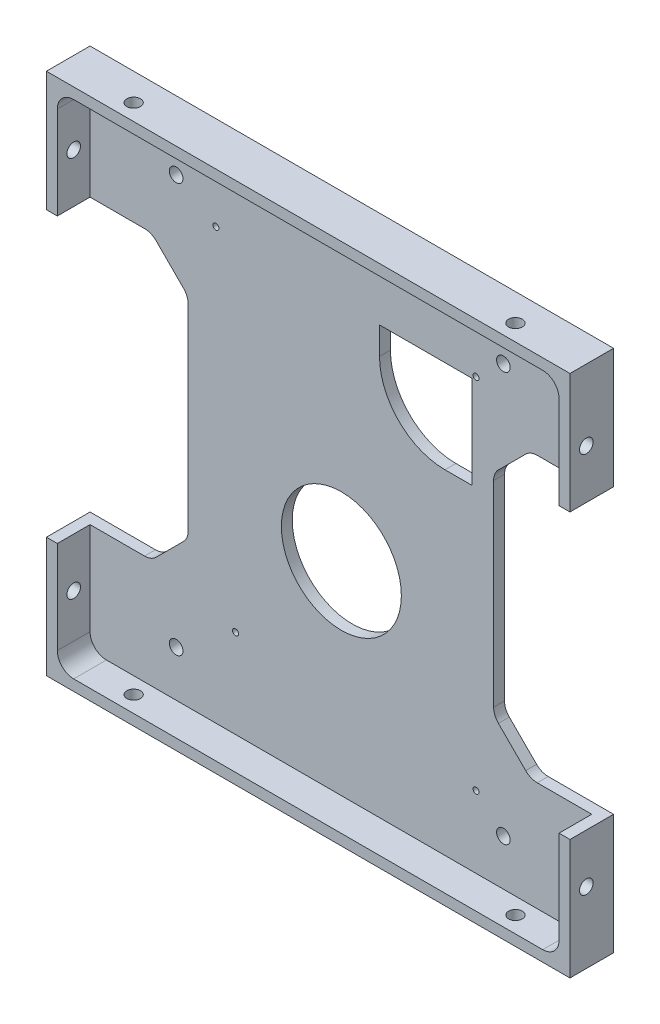
SolidWorks part; units mm, degrees
material "6061-T6 (SS)"
ref_plane "Front" through (0, 0, 0) normal (0, 0, 1) x (1, 0, 0)
ref_plane "Top" through (0, 0, 0) normal (0, 1, 0) x (1, 0, 0)
ref_plane "Right" through (0, 0, 0) normal (1, 0, 0) x (0, 0, -1)
sketch "Sketch1" plane through (0, 0, 0) normal (0, 0, 1) x (1, 0, 0)
  line L1 (-48, -48) -> (48, -48)
  line L2 (-48, -48) -> (-48, 48)
  line L3 (-48, 48) -> (48, 48)
  line L4 (48, -48) -> (48, 48)
  line L5 (-48, -48) -> (48, 48) construction
  line L6 (-48, 48) -> (48, -48) construction
  point P0 (0, 0)
  dimension "D1" = 96
  dimension "D2" = 96
extrude "Boss-Extrude1" add sketch "Sketch1" along normal blind 8
sketch "Sketch2" plane through (0, 0, 8) normal (0, 0, 1) x (1, 0, 0)
  line L1 (46, -46) -> (-46, -46)
  line L2 (46, -46) -> (46, 46)
  line L3 (46, 46) -> (-46, 46)
  line L4 (-46, -46) -> (-46, 46)
  line L5 (46, -46) -> (-46, 46) construction
  line L6 (46, 46) -> (-46, -46) construction
  point P0 (0, 0)
  dimension "D1" = 92
  dimension "D2" = 92
extrude "Component Platform" cut sketch "Sketch2" against normal blind 6
sketch "Sketch3" plane through (0, 0, 2) normal (0, 0, 1) x (1, 0, 0)
  line L1 (-33.8787, -25.1213) -> (-28.8787, -20.1213)
  line L2 (-33.8787, 25.1213) -> (-28.8787, 20.1213)
  line L3 (-28, -18) -> (-28, 18)
  line L4 (-48, -26) -> (-36, -26)
  line L7 (-48, 48) -> (-48, -48) construction
  line L8 (0, -56.7987) -> (0, 73.4321) construction
  line L9 (46, -46) -> (-57.8147, 57.8147) construction
  line L18 (46, 46) -> (-68.5705, -68.5705) construction
  line L23 (-48, 26) -> (-36, 26)
  line L26 (-48, -26) -> (-48, 26)
  line L28 (-48, -48) -> (48, -48) construction
  line L29 (48, -26) -> (48, 26)
  line L30 (48, 26) -> (36, 26)
  line L31 (33.8787, 25.1213) -> (28.8787, 20.1213)
  line L32 (28, -18) -> (28, 18)
  line L33 (33.8787, -25.1213) -> (28.8787, -20.1213)
  line L34 (48, -26) -> (36, -26)
  arc A3 (-28.8787, -20.1213) -> (-28, -18) centre (-31, -18) ccw
  arc A4 (-28.8787, 20.1213) -> (-28, 18) centre (-31, 18) cw
  arc A13 (-33.8787, -25.1213) -> (-36, -26) centre (-36, -23) cw
  arc A15 (-33.8787, 25.1213) -> (-36, 26) centre (-36, 23) ccw
  arc A17 (33.8787, 25.1213) -> (36, 26) centre (36, 23) cw
  arc A18 (28.8787, 20.1213) -> (28, 18) centre (31, 18) ccw
  arc A19 (28.8787, -20.1213) -> (28, -18) centre (31, -18) cw
  arc A20 (33.8787, -25.1213) -> (36, -26) centre (36, -23) ccw
  point P0 (-48, 0)
  point P37 (-48, 0)
  dimension "D2" = 3
  dimension "D3" = 3
  dimension "D4" = 20
  dimension "D6" = 3
  dimension "D7" = 3
  dimension "D8" = 135
  dimension "D5" = 52
  dimension "D9" = 135
  dimension "D10" = 12
  dimension "D11" = 12
  dimension "D12" = 48
extrude "Cable Slots" cut sketch "Sketch3" against normal mid plane 12
ref_plane "Center Y-Plane" through (0, 0, 0) normal (1, 0, 0) x (0, 0, -1)
ref_plane "Center X-Plane" through (0, 0, 0) normal (0, -1, 0) x (-1, 0, 0)
fillet "Inner Corner Fillets" radius 3 4 edges at (46, -46, 5) (-46, -46, 5) (46, 46, 5) (-46, 46, 5)
sketch "Sketch7" plane through (0, 0, 2) normal (0, 0, 1) x (1, 0, 0)
  line L0 (-48, -48) -> (48, -48) construction
  line L4 (48, -48) -> (48, -26) construction
  line L5 (48, 26) -> (48, 48) construction
  line L7 (48, 48) -> (-48, 48) construction
  line L8 (-43, -46) -> (43, -46) construction
  point P1 (-19.32, -29.75)
  point P4 (24.78, -32.85)
  point P5 (24.78, 32.85)
  point P8 (-22.92, 32.85)
  point P12 (24.7, -56.85)
  point P13 (24.7, 48)
  point P14 (-19.4, -48)
  point P15 (48, -32.85)
  point P16 (-48, -32.85)
  point P18 (-19.4, 48)
  point P19 (48, -32.85)
  point P20 (-48, -32.85)
  point P24 (48, 43.7)
  point P25 (-48.7506, 43.7)
  point P27 (48, 32.85)
  point P28 (-23, -48)
  point P29 (-23, 48)
  point P31 (-48.7506, 32.85)
  dimension "D1" = 16.25
  dimension "D2" = 47.7
  dimension "D3" = 15.15
  dimension "D4" = 23.22
  dimension "D5" = 23.22
  dimension "D6" = 44.1
  dimension "D7" = 15.15
  dimension "D8" = 15.15
sketch "Sketch9" plane through (0, 0, 2) normal (0, 0, 1) x (1, 0, 0)
  line L0 (24.08, 32.25) -> (24.08, 15.25)
  line L1 (24.08, 32.25) -> (7.08, 32.25)
  line L3 (24.08, 15.25) -> (19.08, 15.25)
  line L4 (7.08, 27.25) -> (7.08, 32.25)
  line L6 (48, 26) -> (48, 48) construction
  line L8 (48, 48) -> (-48, 48) construction
  arc A0 (7.08, 27.25) -> (19.08, 15.25) centre (19.08, 27.25) ccw
  dimension "D1" = 12
  dimension "D2" = 17
  dimension "D3" = 17
  dimension "D4" = 15.75
  dimension "D5" = 23.92
sketch "Sketch11" plane through (48, 0, 0) normal (1, 0, 0) x (0, 0, -1)
  line L0 (-5, -48) -> (-5, 48) construction
  line L1 (-8, -48) -> (0, -48) construction
  line L2 (-8, 48) -> (0, 48) construction
  line L3 (-8, -48) -> (-8, -26) construction
  dimension "D1" = 3
sketch "Sketch12" plane through (0, 48, 0) normal (0, 1, 0) x (1, 0, 0)
  line L0 (-48, -5) -> (48, -5) construction
  line L1 (-48, -8) -> (-48, 0) construction
  line L2 (48, -8) -> (48, 0) construction
  line L3 (48, -8) -> (-48, -8) construction
  dimension "D1" = 3
hole_wizard "M3x0.5 Tapped Hole1" positions "Sketch13" profile "Sketch14" tap size "M3x0.5" standard "ANSI Metric"
sketch "Sketch13" plane through (48, 0, 0) normal (1, 0, 0) x (0, 0, -1)
  line L0 (-5, -48) -> (-5, 48) construction
  point P0 (-5, -35)
  point P4 (-5, 35)
  dimension "D1" = 70
  dimension "D2" = 35
sketch "Sketch14" plane through (48, -35, 5) normal (0, 1, 0) x (0, 0, -1)
  line L0 (0, 0) -> (0, 10.7511)
  line L1 (0, 10.7511) -> (1.25, 10)
  line L2 (1.25, 10) -> (1.25, 0)
  line L5 (1.25, 0) -> (0, 0)
  line L10 (0, 10.7511) -> (-1.25, 10) construction
  line L11 (0, -6.35) -> (0, 107.95) construction
  dimension "Tap Drill Dia." = 2.5
  dimension "Tap Drill Depth" = 10
  dimension "Drill Angle" = 118
hole_wizard "M3x0.5 Tapped Hole2" positions "Sketch15" profile "Sketch16" tap size "M3x0.5" standard "ANSI Metric"
sketch "Sketch15" plane through (0, 48, 0) normal (0, 1, 0) x (1, 0, 0)
  line L0 (-48, -5) -> (48, -5) construction
  point P0 (35, -5)
  point P4 (-35, -5)
  dimension "D1" = 70
  dimension "D2" = 35
sketch "Sketch16" plane through (35, 48, 5) normal (1, 0, 0) x (0, 0, 1)
  line L0 (0, 0) -> (0, 10.7511)
  line L1 (0, 10.7511) -> (1.25, 10)
  line L2 (1.25, 10) -> (1.25, 0)
  line L5 (1.25, 0) -> (0, 0)
  line L10 (0, 10.7511) -> (-1.25, 10) construction
  line L11 (0, -6.35) -> (0, 107.95) construction
  dimension "Tap Drill Dia." = 2.5
  dimension "Tap Drill Depth" = 10
  dimension "Drill Angle" = 118
mirror "Mirror1" about plane through (0, 0, 0) normal (1, 0, 0) of "M3x0.5 Tapped Hole1"
mirror "Mirror2" about plane through (0, 0, 0) normal (0, -1, 0) of "M3x0.5 Tapped Hole2"
sketch "Sketch22" plane through (0, 0, 2) normal (0, 0, 1) x (1, 0, 0)
  line L0 (-46, -26) -> (-46, -43) construction
  line L1 (-43, -46) -> (43, -46) construction
  line L5 (-46, 43) -> (-46, 26) construction
  line L13 (43, 46) -> (-43, 46) construction
  point P0 (-30.21, -37.56)
  point P1 (-30.21, 37.44)
  point P2 (29.79, 37.44)
  point P3 (29.79, -37.56)
  point P10 (0, 0)
  dimension "D1" = 15.79
  dimension "D2" = 8.44
  dimension "D3" = 75
  dimension "D4" = 15.79
  dimension "D5" = 60
  dimension "D6" = 60
  dimension "D7" = 8.56
  dimension "D8" = 75
hole_wizard "M1.4x0.3 Tapped Hole1" positions "Sketch27" profile "Sketch28" tap size "M1.4x0.3" standard "ANSI Metric"
sketch "Sketch27" plane through (0, 0, 2) normal (0, 0, 1) x (1, 0, 0)
  point P0 (-19.32, -29.75)
  point P3 (24.78, -32.85)
  point P6 (24.78, 32.85)
  point P9 (-22.92, 32.85)
sketch "Sketch28" plane through (-19.32, -29.75, 2) normal (1, 0, 0) x (0, -1, 0)
  line L0 (0, 0) -> (0, 4.0305)
  line L1 (0, 4.0305) -> (0.55, 3.7)
  line L2 (0.55, 3.7) -> (0.55, 0)
  line L5 (0.55, 0) -> (0, 0)
  line L10 (0, 4.0305) -> (-0.55, 3.7) construction
  line L11 (0, -6.35) -> (0, 107.95) construction
  dimension "Tap Drill Dia." = 1.1
  dimension "Tap Drill Depth" = 3.7
  dimension "Drill Angle" = 118
sketch "Sketch29" plane through (0, 0, 0) normal (0, 0, -1) x (-1, 0, 0)
  line L0 (28, 18) -> (28, -18) construction
  line L2 (48, -48) -> (-48, -48) construction
  circle A0 centre (-0.0819, -8.7479) radius 11
  dimension "D1" = 22
  dimension "D2" = 28.0819
  dimension "D3" = 39.2521
extrude "HDD Extrusion Cutout" cut sketch "Sketch29" against normal blind 10
extrude "HDD Extrusion Cutout 2" cut sketch "Sketch9" against normal blind 10
hole_wizard "M3x0.5 Tapped Hole3" positions "Sketch30" profile "Sketch31" tap size "M3x0.5" standard "ANSI Metric"
sketch "Sketch30" plane through (0, 0, 2) normal (0, 0, 1) x (1, 0, 0)
  point P0 (-30.21, -37.56)
  point P3 (29.79, -37.56)
  point P6 (29.79, 37.44)
  point P9 (-30.21, 37.44)
sketch "Sketch31" plane through (-30.21, -37.56, 2) normal (1, 0, 0) x (0, -1, 0)
  line L0 (0, 0) -> (0, 10.7511)
  line L1 (0, 10.7511) -> (1.25, 10)
  line L2 (1.25, 10) -> (1.25, 0)
  line L5 (1.25, 0) -> (0, 0)
  line L10 (0, 10.7511) -> (-1.25, 10) construction
  line L11 (0, -6.35) -> (0, 107.95) construction
  dimension "Tap Drill Dia." = 2.5
  dimension "Tap Drill Depth" = 10
  dimension "Drill Angle" = 118
